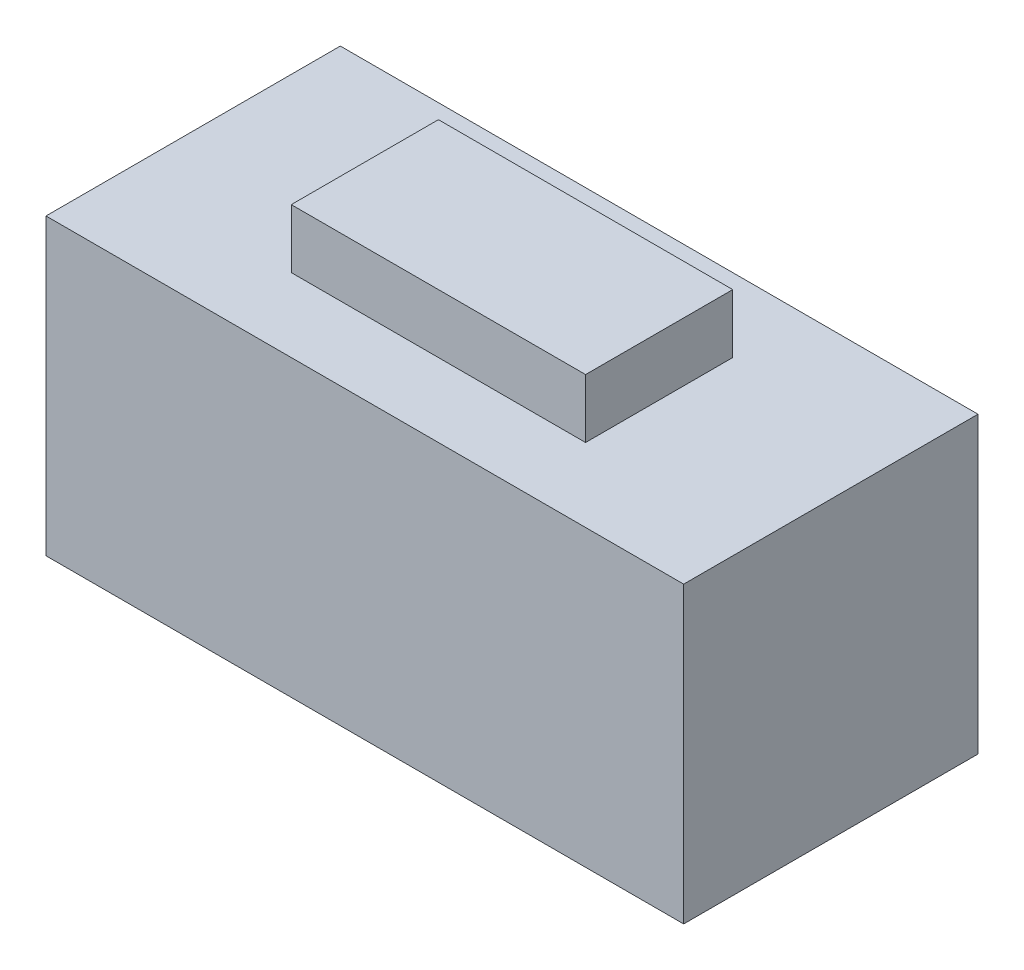
SolidWorks part; units mm, degrees
ref_plane "Front Plane" through (0, 0, 0) normal (0, 0, 1) x (1, 0, 0)
ref_plane "Top Plane" through (0, 0, 0) normal (0, 1, 0) x (1, 0, 0)
ref_plane "Right Plane" through (0, 0, 0) normal (1, 0, 0) x (0, 0, -1)
sketch "Sketch1" plane through (0, 0, 0) normal (0, 1, 0) x (1, 0, 0)
  line L1 (3.25, -1.5) -> (-3.25, -1.5)
  line L2 (3.25, -1.5) -> (3.25, 1.5)
  line L3 (3.25, 1.5) -> (-3.25, 1.5)
  line L4 (-3.25, -1.5) -> (-3.25, 1.5)
  line L5 (3.25, -1.5) -> (-3.25, 1.5) construction
  line L6 (3.25, 1.5) -> (-3.25, -1.5) construction
  point P0 (0, 0)
  dimension "D1" = 6.5
  dimension "D2" = 3
extrude "Boss-Extrude1" add sketch "Sketch1" along normal blind 3
sketch "Sketch2" plane through (0, 3, 0) normal (0, 1, 0) x (1, 0, 0)
  line L1 (1.5, -0.75) -> (-1.5, -0.75)
  line L2 (1.5, -0.75) -> (1.5, 0.75)
  line L3 (1.5, 0.75) -> (-1.5, 0.75)
  line L12 (-1.5, -0.75) -> (-1.5, 0.75)
  line L13 (1.5, -0.75) -> (-1.5, 0.75) construction
  line L14 (1.5, 0.75) -> (-1.5, -0.75) construction
  point P2 (0, 0)
  dimension "D2" = 3
  dimension "D3" = 1.5
extrude "Boss-Extrude2" add sketch "Sketch2" along normal blind 0.6
